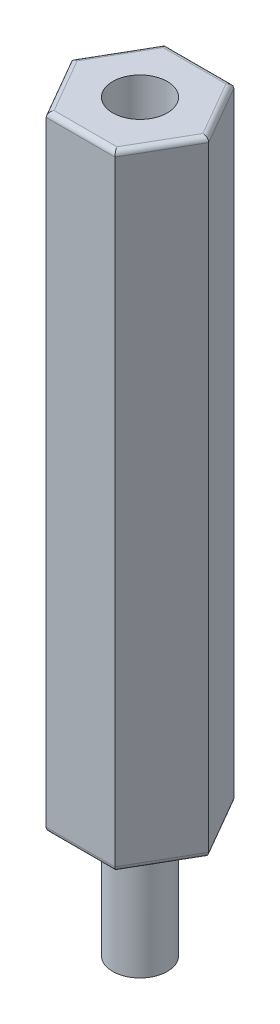
SolidWorks part; units mm, degrees
material "201.0-T43 Molde de fundição com isolamento (SS)"
ref_plane "Plano frontal" through (0, 0, 0) normal (0, 0, 1) x (1, 0, 0)
ref_plane "Plano superior" through (0, 0, 0) normal (0, 1, 0) x (1, 0, 0)
ref_plane "Plano direito" through (0, 0, 0) normal (1, 0, 0) x (0, 0, -1)
sketch "Esboço1" plane through (0, 0, 0) normal (0, 1, 0) x (1, 0, 0)
  line L1 (2.7482, 0) -> (1.3741, 2.38)
  line L2 (1.3741, 2.38) -> (-1.3741, 2.38)
  line L3 (-1.3741, 2.38) -> (-2.7482, 0)
  line L4 (-2.7482, 0) -> (-1.3741, -2.38)
  line L5 (-1.3741, -2.38) -> (1.3741, -2.38)
  line L6 (1.3741, -2.38) -> (2.7482, 0)
  circle A0 centre (0, 0) radius 2.38 construction
  dimension "D1" = 4.76
extrude "Ressalto-extrusão1" add sketch "Esboço1" along normal blind 25
fillet "Filete1" radius 0.2 12 edges at (0, 25, -2.38) (-2.0611, 25, -1.19) (-2.0611, 25, 1.19) (0, 25, 2.38) (2.0611, 25, 1.19) (2.0611, 25, -1.19) (0, 0, 2.38) (-2.0611, 0, 1.19) (-2.0611, 0, -1.19) (0, 0, -2.38) (2.0611, 0, -1.19) (2.0611, 0, 1.19)
sketch "Esboço2" plane through (0, 0, 0) normal (0, -1, 0) x (1, 0, 0)
  circle A0 centre (0, 0) radius 1.0922
  dimension "D1" = 2.1844
extrude "Ressalto-extrusão2" add sketch "Esboço2" along normal blind 4.76
sketch "Esboço3" plane through (0, 25, 0) normal (0, 1, 0) x (1, 0, 0)
  circle A0 centre (0, 0) radius 1.0922
extrude "Corte-extrusão1" cut sketch "Esboço3" against normal blind 4.76
